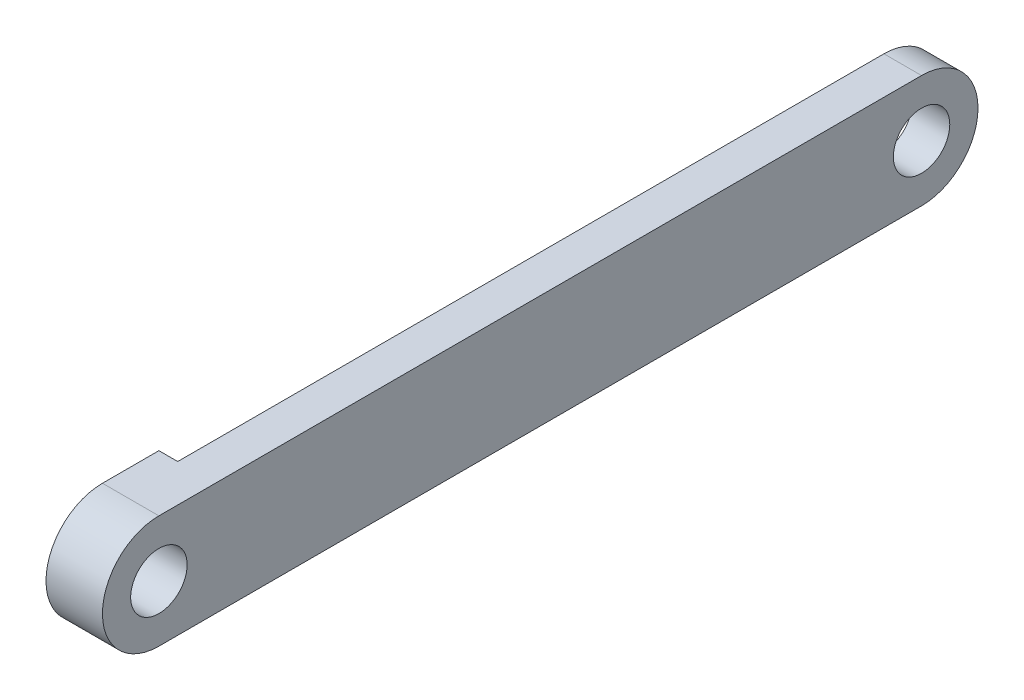
SolidWorks part; units mm, degrees
ref_plane "Front Plane" through (0, 0, 0) normal (0, 0, 1) x (1, 0, 0)
ref_plane "Top Plane" through (0, 0, 0) normal (0, 1, 0) x (1, 0, 0)
ref_plane "Right Plane" through (0, 0, 0) normal (1, 0, 0) x (0, 0, -1)
sketch "Sketch1" plane through (0, 0, 0) normal (1, 0, 0) x (0, 0, -1)
  line L0 (0, 0) -> (40.53, 0) construction
  line L1 (0, -3) -> (40.53, -3)
  line L18 (0, 3) -> (40.53, 3)
  arc A10 (0, -3) -> (0, 3) centre (0, 0) cw
  arc A11 (40.53, 3) -> (40.53, -3) centre (40.53, 0) cw
  circle A12 centre (0, 0) radius 1.5
  circle A13 centre (40.53, 0) radius 1.5
  dimension "D4" = 3
  dimension "D1" = 3
  dimension "D3" = 40.53
  dimension "D2" = 3
extrude "Boss-Extrude1" add sketch "Sketch1" along normal blind 3
sketch "Sketch2" plane through (0, 0, 0) normal (-1, 0, 0) x (0, 0, 1)
  line L0 (0, -3) -> (-40.53, -3) construction
  line L1 (-43.53, 3) -> (-3, 3)
  line L2 (-43.53, 3) -> (-43.53, -3)
  line L3 (-43.53, -3) -> (-3, -3)
  line L4 (-3, 3) -> (-3, -3)
  line L5 (-40.53, 3) -> (0, 3) construction
  arc A0 (0, -3) -> (0, 3) centre (0, 0) ccw construction
  arc A1 (-40.53, 3) -> (-40.53, -3) centre (-40.53, 0) ccw construction
  point P9 (3, 0)
  dimension "D1" = 6
extrude "Cut-Extrude1" cut sketch "Sketch2" against normal blind 1 contours L1 L4 L3 L2
